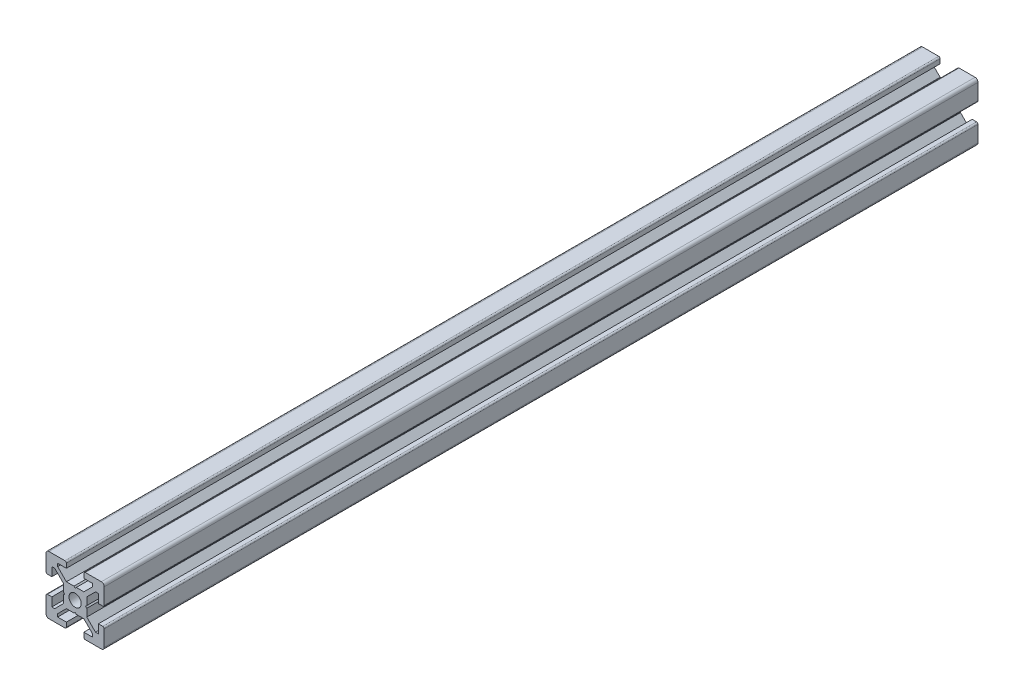
SolidWorks part; units mm, degrees
material "Lega 6061"
ref_plane "Piano frontale" through (0, 0, 0) normal (0, 0, 1) x (1, 0, 0)
ref_plane "Piano superiore" through (0, 0, 0) normal (0, 1, 0) x (1, 0, 0)
ref_plane "Piano destro" through (0, 0, 0) normal (1, 0, 0) x (0, 0, -1)
sketch "Schizzo1" plane through (0, 0, 0) normal (0, 0, 1) x (1, 0, 0)
  line L0 (0, 0) -> (-10, 0) construction
  line L1 (0, 0) -> (0, 10) construction
  line L2 (-3.6, 0) -> (-4, 0.4)
  line L3 (-4, 0.4) -> (-4, 3)
  line L4 (-4, 3) -> (-7, 6)
  line L5 (-7, 6) -> (-8, 6)
  line L6 (-8, 6) -> (-8, 3)
  line L7 (-8, 3) -> (-9.5, 3)
  line L8 (-10, 3.5) -> (-10, 9)
  line L9 (0, 0) -> (-10, 10) construction
  line L10 (0, 3.6) -> (-0.4, 4)
  line L11 (-0.4, 4) -> (-3, 4)
  line L12 (-3, 4) -> (-6, 7)
  line L13 (-6, 7) -> (-6, 8)
  line L14 (-6, 8) -> (-3, 8)
  line L15 (-3, 8) -> (-3, 9.5)
  line L16 (-3.5, 10) -> (-9, 10)
  line L17 (0, 0) -> (-10, -10) construction
  line L18 (-3.5, -10) -> (-9, -10)
  line L19 (-3, -8) -> (-3, -9.5)
  line L20 (-6, -8) -> (-3, -8)
  line L21 (-6, -7) -> (-6, -8)
  line L22 (-3, -4) -> (-6, -7)
  line L23 (-0.4, -4) -> (-3, -4)
  line L24 (0, -3.6) -> (-0.4, -4)
  line L25 (-10, -3.5) -> (-10, -9)
  line L26 (-8, -3) -> (-9.5, -3)
  line L27 (-8, -6) -> (-8, -3)
  line L28 (-7, -6) -> (-8, -6)
  line L29 (-4, -3) -> (-7, -6)
  line L30 (-4, -0.4) -> (-4, -3)
  line L31 (-3.6, 0) -> (-4, -0.4)
  line L32 (0, 0) -> (10, -10) construction
  line L33 (0, 0) -> (10, 10) construction
  line L34 (3.6, 0) -> (4, -0.4)
  line L35 (4, -0.4) -> (4, -3)
  line L36 (4, -3) -> (7, -6)
  line L37 (7, -6) -> (8, -6)
  line L38 (8, -6) -> (8, -3)
  line L39 (8, -3) -> (9.5, -3)
  line L40 (10, -3.5) -> (10, -9)
  line L41 (0, -3.6) -> (0.4, -4)
  line L42 (0.4, -4) -> (3, -4)
  line L43 (3, -4) -> (6, -7)
  line L44 (6, -7) -> (6, -8)
  line L45 (6, -8) -> (3, -8)
  line L46 (3, -8) -> (3, -9.5)
  line L47 (3.5, -10) -> (9, -10)
  line L48 (3.5, 10) -> (9, 10)
  line L49 (3, 8) -> (3, 9.5)
  line L50 (6, 8) -> (3, 8)
  line L51 (6, 7) -> (6, 8)
  line L52 (3, 4) -> (6, 7)
  line L53 (0.4, 4) -> (3, 4)
  line L54 (0, 3.6) -> (0.4, 4)
  line L55 (10, 3.5) -> (10, 9)
  line L56 (8, 3) -> (9.5, 3)
  line L57 (8, 6) -> (8, 3)
  line L58 (7, 6) -> (8, 6)
  line L59 (4, 3) -> (7, 6)
  line L60 (4, 0.4) -> (4, 3)
  line L61 (3.6, 0) -> (4, 0.4)
  arc A0 (-10, 9) -> (-9, 10) centre (-9, 9) cw
  arc A1 (-3, 9.5) -> (-3.5, 10) centre (-3.5, 9.5) ccw
  arc A2 (-9.5, 3) -> (-10, 3.5) centre (-9.5, 3.5) cw
  arc A3 (-9.5, -3) -> (-10, -3.5) centre (-9.5, -3.5) ccw
  arc A4 (-3, -9.5) -> (-3.5, -10) centre (-3.5, -9.5) cw
  arc A5 (-10, -9) -> (-9, -10) centre (-9, -9) ccw
  arc A6 (10, -9) -> (9, -10) centre (9, -9) cw
  arc A7 (3, -9.5) -> (3.5, -10) centre (3.5, -9.5) ccw
  arc A8 (9.5, -3) -> (10, -3.5) centre (9.5, -3.5) cw
  arc A9 (9.5, 3) -> (10, 3.5) centre (9.5, 3.5) ccw
  arc A10 (3, 9.5) -> (3.5, 10) centre (3.5, 9.5) cw
  arc A11 (10, 9) -> (9, 10) centre (9, 9) ccw
  circle A12 centre (0, 0) radius 2.1
  point P24 (-3, 10)
  point P27 (-10, 3)
  point P49 (-10, -3)
  point P50 (-3, -10)
  point P92 (3, -10)
  point P93 (10, -3)
  point P94 (10, 3)
  point P95 (3, 10)
  dimension "D2" = 1
  dimension "D12" = 0.5
  dimension "D13" = 4.2
  dimension "D3" = 8
  dimension "D4" = 0.4
  dimension "D5" = 45
  dimension "D6" = 6
  dimension "D7" = 12
  dimension "D8" = 20
  dimension "D9" = 2
  dimension "D10" = 4
  dimension "D11" = 45
extrude "Estrusione-Estrusione1" add sketch "Schizzo1" along normal blind 300
